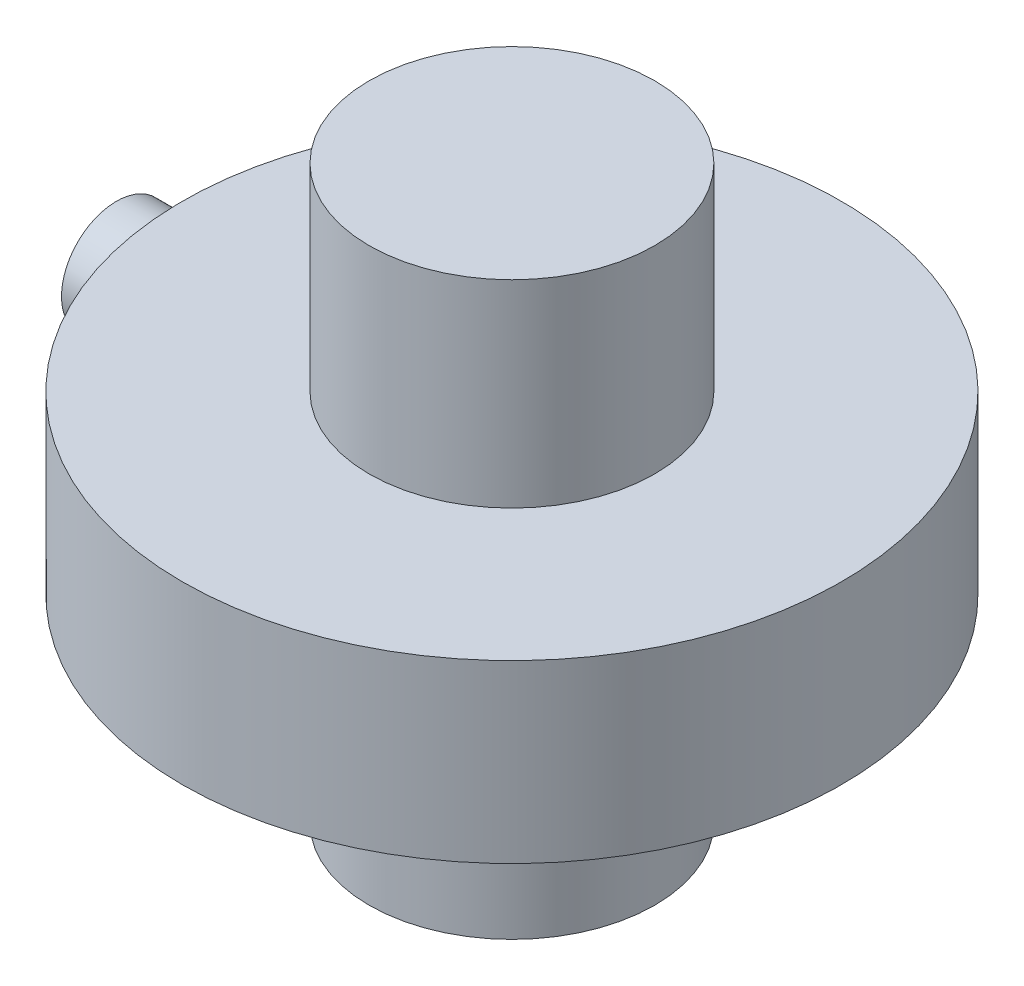
SolidWorks part; units mm, degrees
ref_plane "Front Plane" through (0, 0, 0) normal (0, 0, 1) x (1, 0, 0)
ref_plane "Top Plane" through (0, 0, 0) normal (0, 1, 0) x (1, 0, 0)
ref_plane "Right Plane" through (0, 0, 0) normal (1, 0, 0) x (0, 0, -1)
sketch "Sketch1" plane through (0, 0, 0) normal (1, 0, 0) x (0, 0, -1)
  circle A0 centre (0, 0) radius 5
  dimension "D1" = 10
extrude "Boss-Extrude1" add sketch "Sketch1" along normal blind 10
sketch "Sketch4" plane through (0, 0, 0) normal (0, 1, 0) x (1, 0, 0)
  circle A0 centre (36, 0) radius 30
  dimension "D1" = 60
  dimension "D2" = 36
extrude "Boss-Extrude4" add sketch "Sketch4" along normal mid plane 16 separate body
sketch "Sketch5" plane through (0, 0, 0) normal (0, 1, 0) x (1, 0, 0)
  circle A0 centre (36, 0) radius 13
  circle A1 centre (36, 0) radius 30 construction
  dimension "D1" = 26
extrude "Boss-Extrude5" add sketch "Sketch5" along normal mid plane 52
